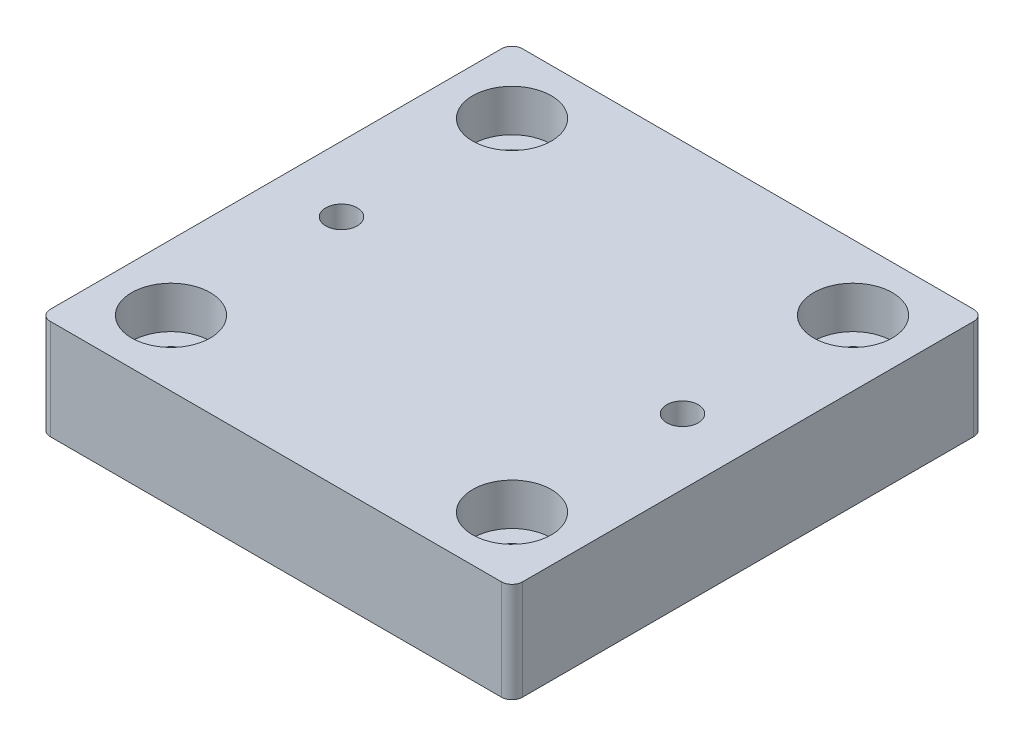
SolidWorks part; units mm, degrees
ref_plane "Front Plane" through (0, 0, 0) normal (0, 0, 1) x (1, 0, 0)
ref_plane "Top Plane" through (0, 0, 0) normal (0, 1, 0) x (1, 0, 0)
ref_plane "Right Plane" through (0, 0, 0) normal (1, 0, 0) x (0, 0, -1)
sketch "Sketch1" plane through (0, 0, 0) normal (0, 1, 0) x (1, 0, 0)
  line L0 (-32.5, 32.5) -> (-32.5, -32.5) construction
  line L1 (-43, -45) -> (43, -45)
  line L2 (-45, -43) -> (-45, 43)
  line L3 (-43, 45) -> (43, 45)
  line L4 (45, -43) -> (45, 43)
  line L5 (32.5, 32.5) -> (32.5, -32.5) construction
  arc A0 (-43, -45) -> (-45, -43) centre (-43, -43) cw
  arc A1 (43, -45) -> (45, -43) centre (43, -43) ccw
  arc A2 (43, 45) -> (45, 43) centre (43, 43) cw
  arc A3 (-45, 43) -> (-43, 45) centre (-43, 43) cw
  circle A4 centre (-32.5, 32.5) radius 12.5 construction
  circle A5 centre (-32.5, -32.5) radius 12.5 construction
  circle A6 centre (32.5, -32.5) radius 12.5 construction
  circle A7 centre (32.5, 32.5) radius 12.5 construction
  circle A8 centre (-32.5, 32.5) radius 4
  circle A9 centre (32.5, 32.5) radius 4
  circle A10 centre (32.5, -32.5) radius 4
  circle A11 centre (-32.5, -32.5) radius 4
  circle A12 centre (-32.5, 32.5) radius 7.5 construction
  circle A13 centre (32.5, 32.5) radius 7.5 construction
  circle A14 centre (-32.5, -32.5) radius 7.5 construction
  circle A15 centre (32.5, -32.5) radius 7.5 construction
  circle A16 centre (-32.5, 0) radius 3
  circle A17 centre (32.5, 0) radius 3
  point P0 (0, 0)
  point P2 (0, 45)
  point P3 (-45, 0)
  dimension "D1" = 2
  dimension "D4" = 15
  dimension "D6" = 8
  dimension "D7" = 6
  dimension "D2" = 90
  dimension "D3" = 90
  dimension "D5" = 65
extrude "Boss-Extrude1" add sketch "Sketch1" along normal blind 19.05
sketch "Sketch2" plane through (0, 19.05, 0) normal (0, 1, 0) x (1, 0, 0)
  circle A0 centre (-32.5, -32.5) radius 7.5 construction
  circle A1 centre (32.5, -32.5) radius 7.5 construction
  circle A2 centre (32.5, 32.5) radius 7.5 construction
  circle A3 centre (-32.5, 32.5) radius 7.5 construction
  circle A4 centre (-32.5, -32.5) radius 7.5
  circle A5 centre (32.5, -32.5) radius 7.5
  circle A6 centre (32.5, 32.5) radius 7.5
  circle A7 centre (-32.5, 32.5) radius 7.5
extrude "Cut-Extrude1" cut sketch "Sketch2" against normal blind 8
equation "\"D3@Sketch1\"=\"D2@Sketch1\""
